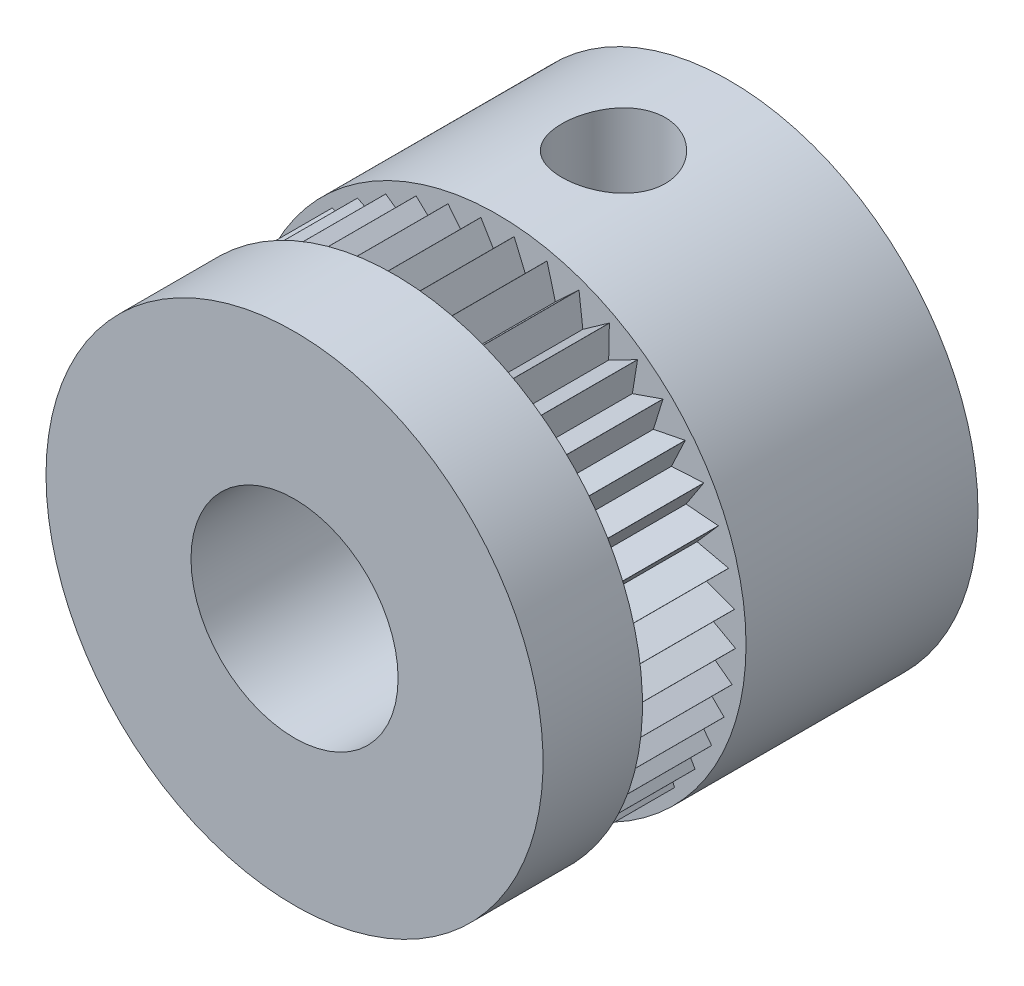
SolidWorks part; units mm, degrees
ref_plane "Alzado" through (0, 0, 0) normal (0, 0, 1) x (1, 0, 0)
ref_plane "Planta" through (0, 0, 0) normal (0, 1, 0) x (1, 0, 0)
ref_plane "Vista lateral" through (0, 0, 0) normal (1, 0, 0) x (0, 0, -1)
sketch "Croquis1" plane through (0, 0, 0) normal (0, 0, 1) x (1, 0, 0)
  circle A0 centre (0, 0) radius 6
  circle A1 centre (0, 0) radius 2.5
  dimension "D1" = 12
  dimension "D2" = 5
extrude "Saliente-Extruir1" add sketch "Croquis1" along normal blind 10.5
ref_axis "Eje1" through (0, 0, 10.5) along (0, 0, -1)
sketch "Croquis2" plane through (0, 0, 0) normal (0, 1, 0) x (1, 0, 0)
  line L0 (6, -5.6) -> (5.75, -5.6)
  line L1 (6, -10.5) -> (6, 0) construction
  line L2 (5.75, -5.6) -> (5.75, -8.1)
  line L3 (5.75, -8.1) -> (6, -8.1)
  line L4 (6, -8.1) -> (6, -5.6)
  line L5 (6, 0) -> (-6, 0) construction
  dimension "D1" = 5.6
  dimension "D2" = 2.5
  dimension "D3" = 0.25
revolve "Cortar-Revolución1" cut sketch "Croquis2" angle 360 about axis through (0, 0, 10.5) along (0, 0, -1)
sketch "Croquis3" plane through (0, 0, 8.1) normal (0, 0, -1) x (-1, 0, 0)
  line L0 (0, 5.75) -> (0, 2.5) construction
  line L5 (-0.4, 5.7361) -> (0, 5.0647)
  line L6 (0, 5.0647) -> (0.4, 5.7361)
  circle A0 centre (0, 0) radius 5.75 construction
  circle A1 centre (0, 0) radius 2.5 construction
  arc A2 (0.4, 5.7361) -> (-0.4, 5.7361) centre (0, 0) ccw
extrude "Cortar-Extruir1" cut sketch "Croquis3" along direction (0, 0, -1) on the side of the normal up to surface (2.5 mm away)
pattern_circular "MatrizC1" count 45 over 360 about axis through (0, 0, 0) along (0, 0, 1) of "Cortar-Extruir1"
ref_plane "Plano1" through (0, 6, 0) normal (0, 1, 0) x (1, 0, 0)
hole_wizard "Perforador para roscar para macho de roscar para M31" positions "Croquis5" profile "Croquis4" hole size "M3" standard "ISO"
sketch "Croquis5" plane through (0, 6, 0) normal (0, 1, 0) x (1, 0, 0)
  line L0 (-6, -2.8) -> (6, -2.8) construction
  line L1 (-6, 0) -> (-6, -5.6) construction
  line L2 (6, -5.6) -> (6, 0) construction
  point P0 (0, -2.8)
sketch "Croquis4" plane through (0, 6, 2.8) normal (1, 0, 0) x (0, 0, 1)
  line L0 (0, 0) -> (0, 3.5)
  line L1 (0, 3.5) -> (1.25, 3.5)
  line L2 (1.25, 3.5) -> (1.25, 0)
  line L5 (1.25, 0) -> (0, 0)
  line L11 (0, -6.35) -> (0, 107.95) construction
  dimension "Diámetro de taladro hasta el siguiente" = 2.5
  dimension "Profundidad de taladro hasta el siguiente" = 3.5
